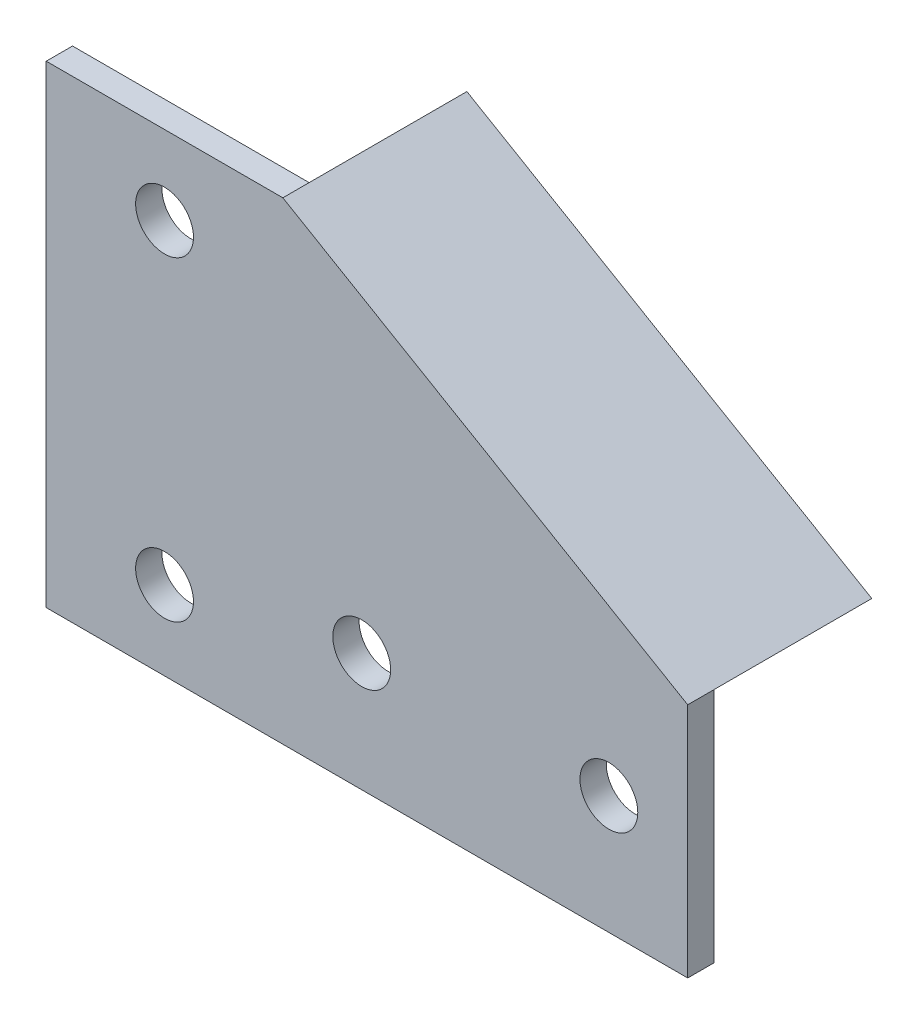
SolidWorks part; units mm, degrees
ref_plane "Plan de face" through (0, 0, 0) normal (0, 0, 1) x (1, 0, 0)
ref_plane "Plan de dessus" through (0, 0, 0) normal (0, 1, 0) x (1, 0, 0)
ref_plane "Plan de droite" through (0, 0, 0) normal (1, 0, 0) x (0, 0, -1)
sketch "Esquisse1" plane through (0, 0, 0) normal (0, 0, 1) x (1, 0, 0)
  line L0 (0, 0) -> (0, 90)
  line L1 (0, 90) -> (45, 90)
  line L2 (45, 90) -> (122, 45)
  line L3 (122, 45) -> (122, 0)
  line L4 (122, 0) -> (0, 0)
  line L5 (22.5, 90) -> (22.5, 22.5) construction
  line L6 (22.5, 22.5) -> (122, 22.5) construction
  circle A1 centre (22.5, 75) radius 5.5
  circle A2 centre (22.5, 15) radius 5.5
  circle A3 centre (107, 22.5) radius 5.5
  circle A4 centre (60, 22.5) radius 5.5
  dimension "D5" = 11
  dimension "D6" = 11
  dimension "D7" = 15
  dimension "D8" = 15
  dimension "D9" = 15
  dimension "D10" = 11
  dimension "D11" = 11
  dimension "D12" = 60
  dimension "D13" = 22.5
  dimension "D1" = 90
  dimension "D2" = 77
  dimension "D3" = 45
  dimension "D4" = 45
extrude "Boss.-Extru.1" add sketch "Esquisse1" along normal blind 5
sketch "Esquisse2" plane through (0, 0, 0) normal (0, 0, 1) x (1, 0, 0)
  line L0 (22.5, 75) -> (22.5, 15) construction
  line L1 (107, 22.5) -> (60, 22.5) construction
  line L3 (17.5, 64) -> (27.5, 64)
  line L4 (17.5, 64) -> (17.5, 26)
  line L5 (17.5, 26) -> (27.5, 26)
  line L6 (27.5, 64) -> (27.5, 26)
  line L7 (71, 27.5) -> (96, 27.5)
  line L8 (71, 27.5) -> (71, 17.5)
  line L9 (71, 17.5) -> (96, 17.5)
  line L10 (96, 27.5) -> (96, 17.5)
  dimension "D1" = 10
  dimension "D2" = 5
  dimension "D3" = 11
  dimension "D4" = 11
  dimension "D5" = 5
  dimension "D6" = 10
  dimension "D7" = 11
  dimension "D8" = 11
extrude "Boss.-Extru.2" add sketch "Esquisse2" against normal blind 6
draft "Dépouille3" type of draft neutral plane draft angle 10 faces to draft 8 face at (83.5, 27.5, -3) face at (96, 22.5, -3) face at (71, 22.5, -3) face at (83.5, 17.5, -3) face at (22.5, 26, -3) face at (27.5, 45, -3) face at (22.5, 64, -3) face at (17.5, 45, -3) neutral plane through (0, 0, 0) neutral plane normal (0, 0, -1) parameters "D1"=10
chamfer "Chanfrein2" [suppressed] distance 5 angle 45
sketch "Esquisse3" plane through (0, 0, 0) normal (0, 0, -1) x (-1, 0, 0)
  line L0 (-122, 45) -> (-45, 45)
  line L1 (-45, 45) -> (-45, 90)
  line L2 (-45, 90) -> (-122, 45)
extrude "Boss.-Extru.3" add sketch "Esquisse3" along normal blind 30
chamfer "Chanfrein3" distance 5 angle 45 1 edges at (45, 45, -15)
